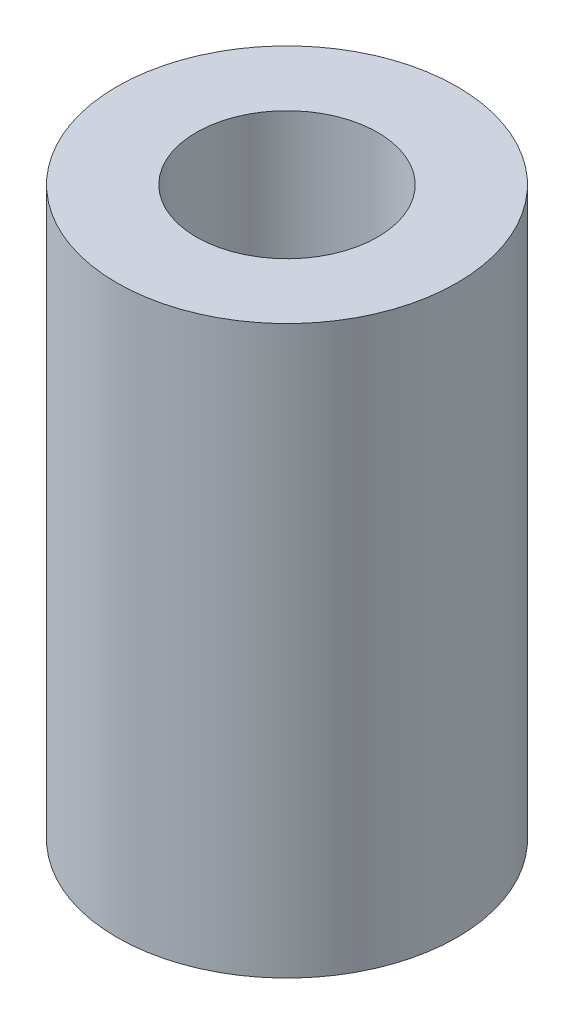
SolidWorks part; units mm, degrees
ref_plane "Front Plane" through (0, 0, 0) normal (0, 0, 1) x (1, 0, 0)
ref_plane "Top Plane" through (0, 0, 0) normal (0, 1, 0) x (1, 0, 0)
ref_plane "Right Plane" through (0, 0, 0) normal (1, 0, 0) x (0, 0, -1)
sketch "Sketch1" plane through (0, 0, 0) normal (0, 1, 0) x (1, 0, 0)
  circle A0 centre (0, 0) radius 7.5
  circle A1 centre (0, 0) radius 4
  dimension "D1" = 15
  dimension "D2" = 8
extrude "Boss-Extrude1" add sketch "Sketch1" along normal blind 25
